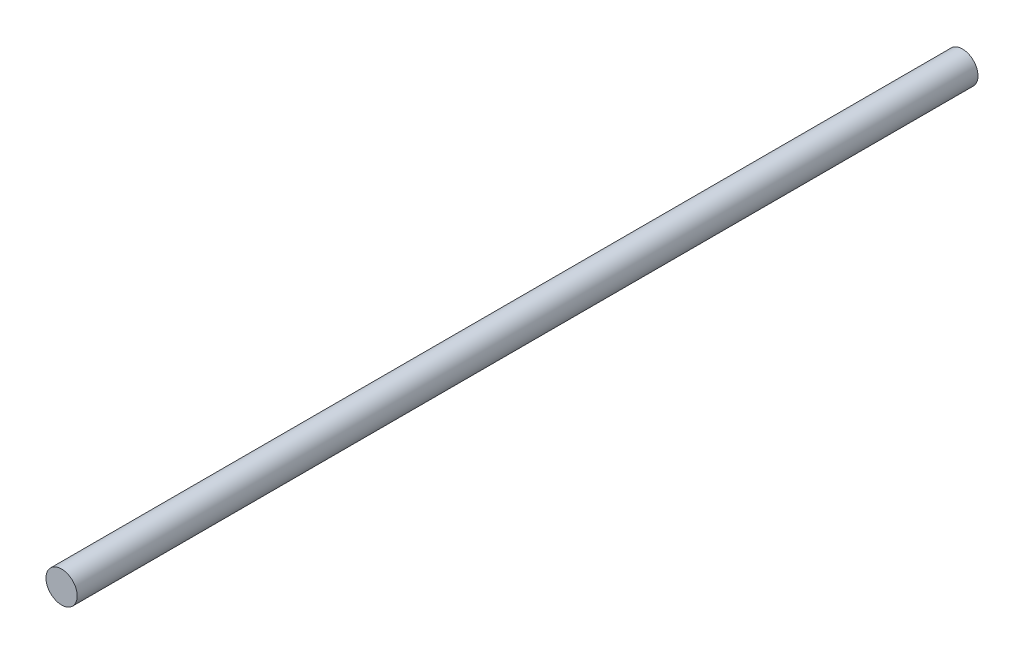
SolidWorks part; units mm, degrees
ref_plane "Front Plane" through (0, 0, 0) normal (0, 0, 1) x (1, 0, 0)
ref_plane "Top Plane" through (0, 0, 0) normal (0, 1, 0) x (1, 0, 0)
ref_plane "Right Plane" through (0, 0, 0) normal (1, 0, 0) x (0, 0, -1)
sketch "Sketch1" plane through (0, 0, 0) normal (0, 0, 1) x (1, 0, 0)
  circle A0 centre (0, 0) radius 5
  dimension "D1" = 10
extrude "Boss-Extrude1" add sketch "Sketch1" along normal blind 288.5
